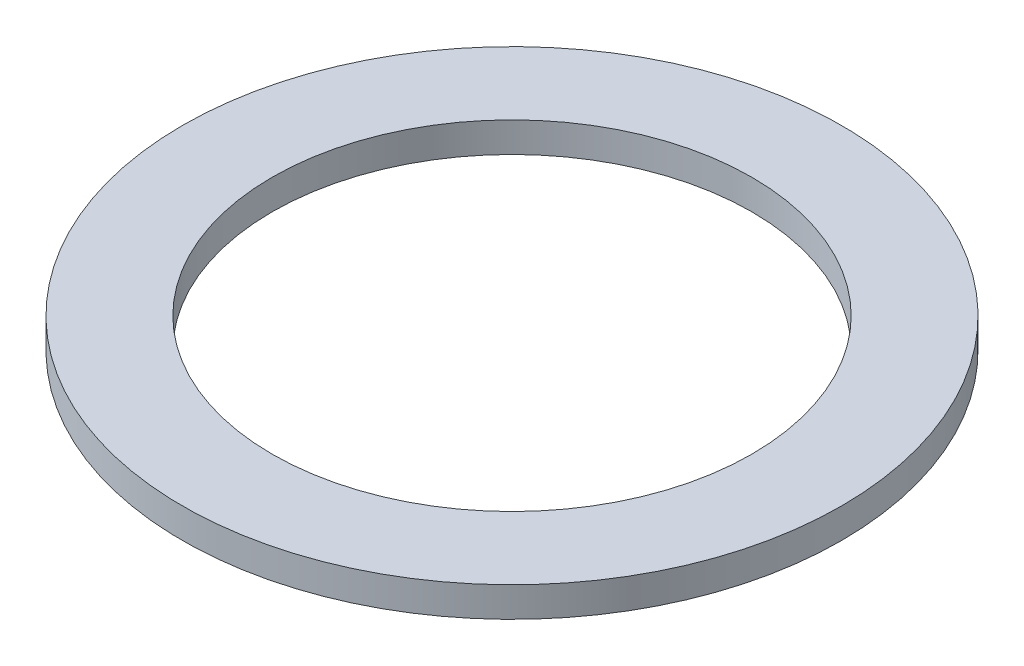
SolidWorks part; units mm, degrees
material "Phenolic Sheet Stock"
ref_plane "Front Plane" through (0, 0, 0) normal (0, 0, 1) x (1, 0, 0)
ref_plane "Top Plane" through (0, 0, 0) normal (0, 1, 0) x (1, 0, 0)
ref_plane "Right Plane" through (0, 0, 0) normal (1, 0, 0) x (0, 0, -1)
sketch "Sketch1" plane through (0, 0, 0) normal (0, 0, 1) x (1, 0, 0)
  line L0 (0, 0) -> (0, 3.175) construction
  line L1 (0, 3.175) -> (-34.8996, 3.175) construction
  line L2 (-34.8996, 3.175) -> (-34.8996, 0)
  line L3 (-34.8996, 0) -> (-25.4, 0)
  line L4 (-25.4, 0) -> (-25.4, 3.175)
  line L5 (-34.8996, 3.175) -> (-25.4, 3.175)
  dimension "D1" = 34.8996
  dimension "D2" = 3.175
  dimension "D3" = 25.4
  dimension "D5" = 0
revolve "Revolve1" add sketch "Sketch1" angle 360 about L0
